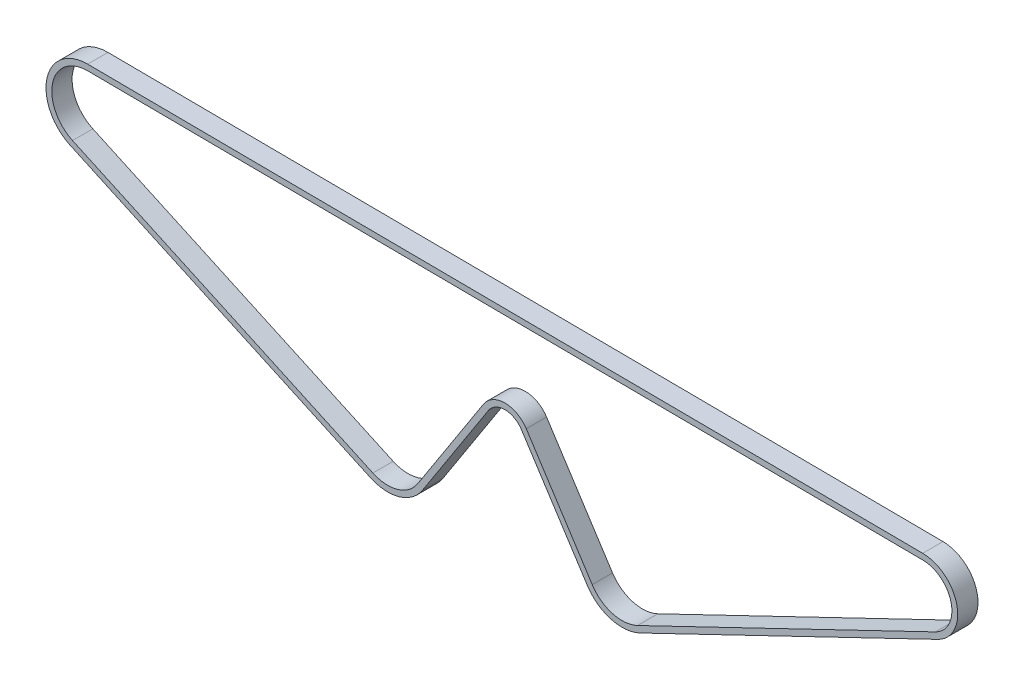
SolidWorks part; units mm, degrees
ref_plane "Front Plane" through (0, 0, 0) normal (0, 0, 1) x (1, 0, 0)
ref_plane "Top Plane" through (0, 0, 0) normal (0, 1, 0) x (1, 0, 0)
ref_plane "Right Plane" through (0, 0, 0) normal (1, 0, 0) x (0, 0, -1)
sketch "Sketch2" plane through (0, 0, 0) normal (0, 0, 1) x (1, 0, 0)
  line L0 (0, 0) -> (1, 0) construction
  line L1 (0, 0) -> (0, 1) construction
  line L2 (148.348, 14.5954) -> (45.7219, -34.8058)
  line L3 (30.0947, -30.4099) -> (7.3657, 4.7602)
  line L4 (-7.3657, 4.7602) -> (-30.0947, -30.4099)
  line L5 (-45.5162, -34.9024) -> (-149.0575, 12.5976)
  line L6 (-143.8513, 36.0197) -> (144.0157, 33.9097)
  arc A0 (144.0157, 33.9097) -> (148.348, 14.5954) centre (143.9413, 23.75) cw
  arc A1 (45.7219, -34.8058) -> (30.0947, -30.4099) centre (40.4, -23.75) cw
  arc A2 (7.3657, 4.7602) -> (-7.3657, 4.7602) centre (0, 0) ccw
  arc A3 (-30.0947, -30.4099) -> (-45.5162, -34.9024) centre (-40.4, -23.75) cw
  arc A4 (-149.0575, 12.5976) -> (-143.8513, 36.0197) centre (-143.9413, 23.75) cw
sketch "Sketch4" plane through (0, 0, 0) normal (0, 0, 1) x (1, 0, 0)
  line L0 (-143.8513, 36.0197) -> (144.0157, 33.9097) construction
  line L1 (-45.5162, -34.9024) -> (-149.0575, 12.5976) construction
  line L2 (-7.3657, 4.7602) -> (-30.0947, -30.4099) construction
  line L3 (30.0947, -30.4099) -> (7.3657, 4.7602) construction
  line L4 (148.348, 14.5954) -> (45.7219, -34.8058) construction
  line L5 (-143.8513, 36.0197) -> (144.0157, 33.9097)
  line L6 (-45.5162, -34.9024) -> (-149.0575, 12.5976)
  line L7 (-7.3657, 4.7602) -> (-30.0947, -30.4099)
  line L8 (30.0947, -30.4099) -> (7.3657, 4.7602)
  line L9 (148.348, 14.5954) -> (45.7219, -34.8058)
  line L10 (149.2155, 12.7933) -> (46.5894, -36.6078)
  line L11 (28.415, -31.4954) -> (5.686, 3.6746)
  line L12 (-5.686, 3.6746) -> (-28.415, -31.4954)
  line L13 (-46.3502, -36.7203) -> (-149.8914, 10.7797)
  line L14 (-143.8367, 38.0196) -> (144.0304, 35.9097)
  arc A0 (148.348, 14.5954) -> (144.0157, 33.9097) centre (143.9413, 23.75) ccw construction
  arc A1 (-143.8513, 36.0197) -> (-149.0575, 12.5976) centre (-143.9413, 23.75) ccw construction
  arc A2 (-45.5162, -34.9024) -> (-30.0947, -30.4099) centre (-40.4, -23.75) ccw construction
  arc A3 (7.3657, 4.7602) -> (-7.3657, 4.7602) centre (0, 0) ccw construction
  arc A4 (30.0947, -30.4099) -> (45.7219, -34.8058) centre (40.4, -23.75) ccw construction
  arc A5 (148.348, 14.5954) -> (144.0157, 33.9097) centre (143.9413, 23.75) ccw
  arc A6 (-143.8513, 36.0197) -> (-149.0575, 12.5976) centre (-143.9413, 23.75) ccw
  arc A7 (-45.5162, -34.9024) -> (-30.0947, -30.4099) centre (-40.4, -23.75) ccw
  arc A8 (7.3657, 4.7602) -> (-7.3657, 4.7602) centre (0, 0) ccw
  arc A9 (30.0947, -30.4099) -> (45.7219, -34.8058) centre (40.4, -23.75) ccw
  arc A10 (28.415, -31.4954) -> (46.5894, -36.6078) centre (40.4, -23.75) ccw
  arc A11 (5.686, 3.6746) -> (-5.686, 3.6746) centre (0, 0) ccw
  arc A12 (-46.3502, -36.7203) -> (-28.415, -31.4954) centre (-40.4, -23.75) ccw
  arc A13 (-143.8367, 38.0196) -> (-149.8914, 10.7797) centre (-143.9413, 23.75) ccw
  arc A14 (149.2155, 12.7933) -> (144.0304, 35.9097) centre (143.9413, 23.75) ccw
  dimension "D1" = 2
extrude "Boss-Extrude1" add sketch "Sketch4" along normal blind 7
